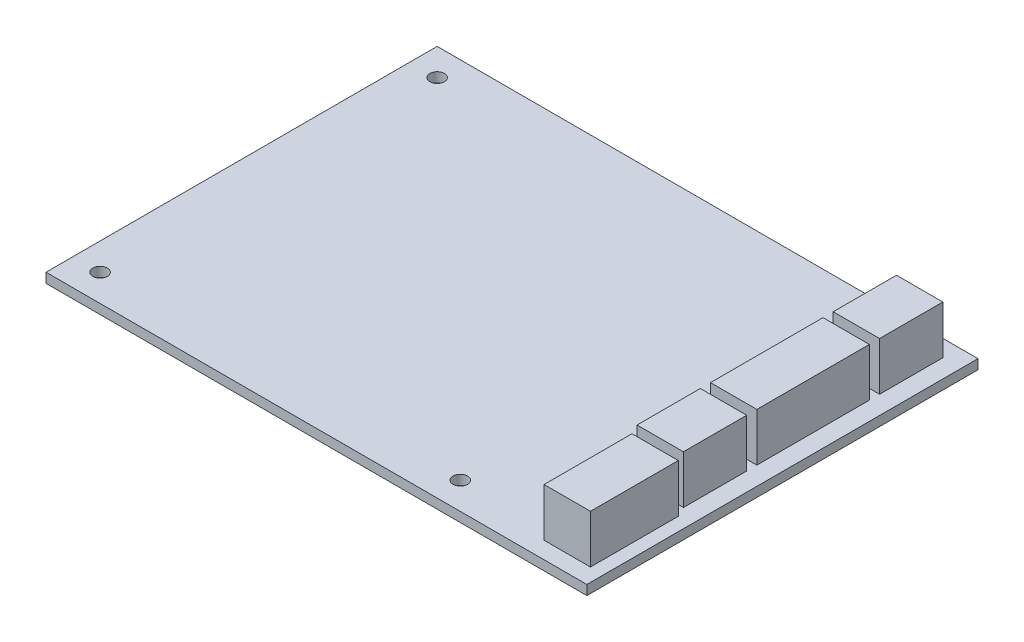
SolidWorks part; units mm, degrees
material "Cuivre"
ref_plane "Plan de face" through (0, 0, 0) normal (0, 0, 1) x (1, 0, 0)
ref_plane "Plan de dessus" through (0, 0, 0) normal (0, 1, 0) x (1, 0, 0)
ref_plane "Plan de droite" through (0, 0, 0) normal (1, 0, 0) x (0, 0, -1)
sketch "Esquisse1" plane through (0, 0, 0) normal (0, 1, 0) x (1, 0, 0)
  line L1 (-56, -40.5) -> (56, -40.5)
  line L2 (-56, -40.5) -> (-56, 40.5)
  line L3 (-56, 40.5) -> (56, 40.5)
  line L4 (56, -40.5) -> (56, 40.5)
  line L5 (-56, -40.5) -> (56, 40.5) construction
  line L6 (-56, 40.5) -> (56, -40.5) construction
  point P0 (0, 0)
  dimension "D1" = 112
  dimension "D2" = 81
extrude "Boss.-Extru.1" add sketch "Esquisse1" along normal blind 2
sketch "Esquisse2" plane through (0, 2, 0) normal (0, 1, 0) x (1, 0, 0)
  line L0 (56, 40.5) -> (-56, 40.5) construction
  line L1 (-56, 40.5) -> (-56, -40.5) construction
  circle A0 centre (-50.4, 34.9) radius 1.5
  circle A1 centre (-50.4, -34.9) radius 1.5
  circle A2 centre (24.2, -34.9) radius 1.5
  circle A3 centre (37.7, 18.1) radius 1.5
  dimension "D9" = 3
  dimension "D10" = 3
  dimension "D11" = 3
  dimension "D12" = 3
  dimension "D1" = 5.6
  dimension "D2" = 5.6
  dimension "D3" = 5.6
  dimension "D4" = 75.4
  dimension "D5" = 80.2
  dimension "D6" = 75.4
  dimension "D7" = 93.7
extrude "Enlèv. mat.-Extru.1" cut sketch "Esquisse2" against normal blind 10
sketch "Esquisse3" plane through (0, 2, -2) normal (0, -1, 0) x (1, 0, 0)
  line L0 (56, -38.5) -> (-56, -38.5) construction
  line L1 (56, 42.5) -> (56, -38.5) construction
  line L3 (42.6, 18.7) -> (52.2, 18.7)
  line L4 (42.6, 18.7) -> (42.6, 5.6)
  line L5 (42.6, 5.6) -> (52.2, 5.6)
  line L6 (52.2, 18.7) -> (52.2, 5.6)
  line L7 (42.6, 3.5) -> (52.2, 3.5)
  line L8 (42.6, 3.5) -> (42.6, -19.8)
  line L9 (42.6, -19.8) -> (52.2, -19.8)
  line L10 (52.2, 3.5) -> (52.2, -19.8)
  line L11 (42.6, -21.92) -> (52.2, -21.92)
  line L12 (42.6, -21.92) -> (42.6, -35.02)
  line L13 (42.6, -35.02) -> (52.2, -35.02)
  line L14 (52.2, -21.92) -> (52.2, -35.02)
  line L15 (43.642, 39) -> (53.242, 39)
  line L16 (43.642, 39) -> (43.642, 20.8)
  line L17 (43.642, 20.8) -> (53.242, 20.8)
  line L18 (53.242, 39) -> (53.242, 20.8)
  point P0 (0, 0)
  point P2 (0, 0)
  point P3 (0, 0)
  point P6 (0, 0)
  dimension "D3" = 98.6
  dimension "D4" = 3.48
  dimension "D5" = 18.7
  dimension "D6" = 44.1
  dimension "D7" = 59.3
  dimension "D8" = 12.358
  dimension "D13" = 9.6
  dimension "D14" = 13.1
  dimension "D19" = 23.3
  dimension "D20" = 18.2
extrude "Boss.-Extru.2" add sketch "Esquisse3" against normal blind 10
